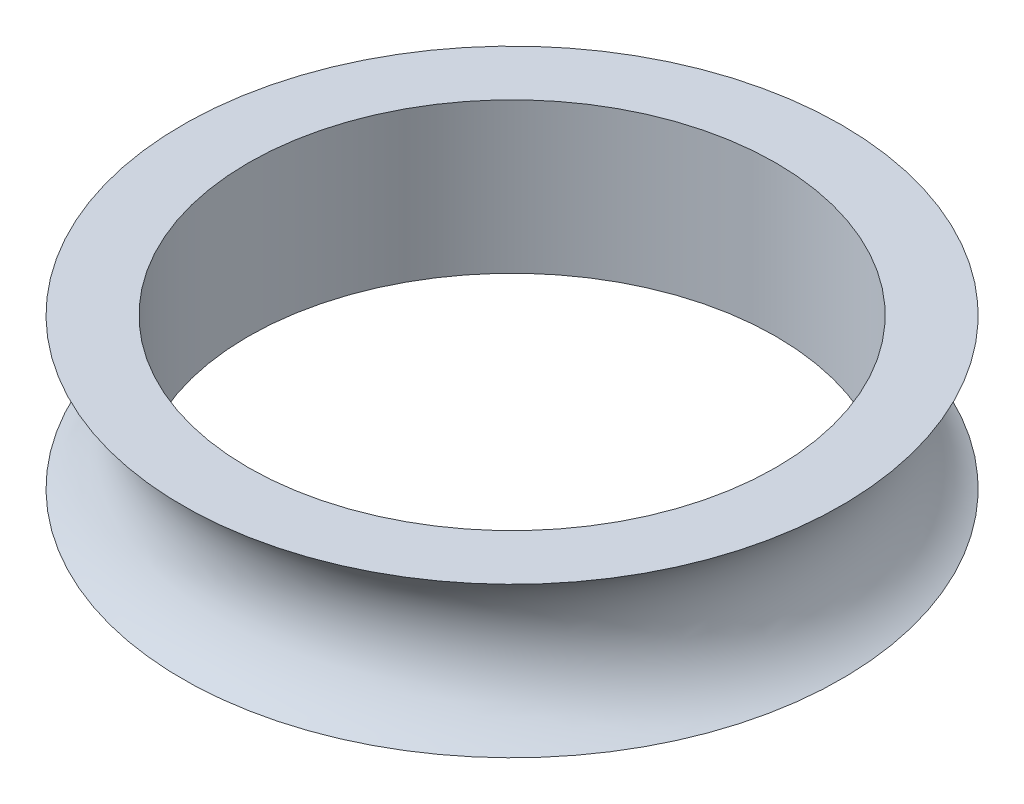
SolidWorks part; units mm, degrees
ref_plane "Front Plane" through (0, 0, 0) normal (0, 0, 1) x (1, 0, 0)
ref_plane "Top Plane" through (0, 0, 0) normal (0, 1, 0) x (1, 0, 0)
ref_plane "Right Plane" through (0, 0, 0) normal (1, 0, 0) x (0, 0, -1)
sketch "Sketch1" plane through (0, 0, 0) normal (0, 0, 1) x (1, 0, 0)
  line L0 (0, 0) -> (0, 15.1026) construction
  line L2 (14.05, 0) -> (17.55, 0)
  line L3 (14.05, 0) -> (14.05, 8)
  line L4 (14.05, 8) -> (17.55, 8)
  arc A0 (17.55, 8) -> (17.55, 0) centre (19.6116, 4) ccw
  dimension "D4" = 9
  dimension "D1" = 14.05
  dimension "D2" = 8
  dimension "D3" = 3.5
revolve "Revolve1" add sketch "Sketch1" angle 360 about L0
